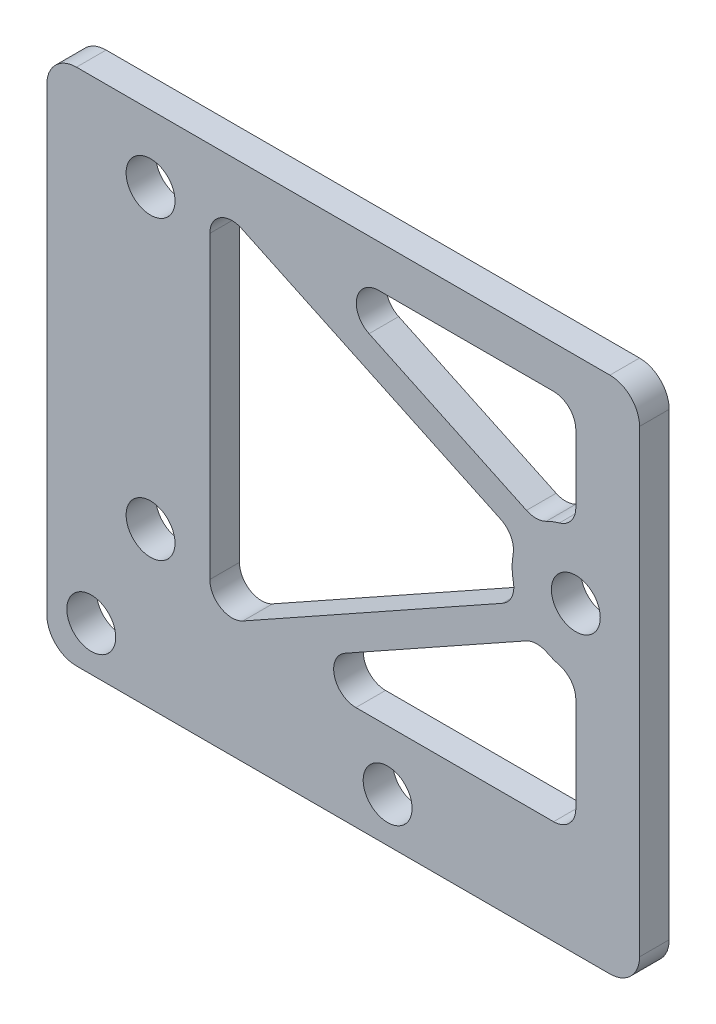
SolidWorks part; units mm, degrees
material "Thornel Mat VMA"
ref_plane "前视基准面" through (0, 0, 0) normal (0, 0, 1) x (1, 0, 0)
ref_plane "上视基准面" through (0, 0, 0) normal (0, 1, 0) x (1, 0, 0)
ref_plane "右视基准面" through (0, 0, 0) normal (1, 0, 0) x (0, 0, -1)
sketch "草图1" plane through (0, 0, 0) normal (0, 0, 1) x (1, 0, 0)
  line L1 (-20, 17.5) -> (20, 17.5)
  line L2 (-20, 17.5) -> (-20, -17.5)
  line L3 (-20, -17.5) -> (20, -17.5)
  line L4 (20, 17.5) -> (20, -17.5)
  line L5 (-20, 17.5) -> (20, -17.5) construction
  line L6 (-20, -17.5) -> (20, 17.5) construction
  point P0 (0, 0)
  dimension "D1" = 40
  dimension "D2" = 35
extrude "凸台-拉伸1" add sketch "草图1" along normal blind 2
sketch "草图2" plane through (0, 0, 2) normal (0, 0, 1) x (1, 0, 0)
  line L0 (-20, -14.5) -> (3, -14.5) construction
  line L1 (-20, 17.5) -> (-20, -17.5) construction
  line L2 (-20, -17.5) -> (20, -17.5) construction
  circle A0 centre (-17, -14.5) radius 1.65
  circle A1 centre (3, -14.5) radius 1.65
  circle A2 centre (-13, -7) radius 1.65
  circle A3 centre (-13, 13) radius 1.65
  circle A4 centre (15.7, 3) radius 1.65
  dimension "D1" = 3.3
  dimension "D3" = 20
  dimension "D5" = 28.7
  dimension "D6" = 4
  dimension "D2" = 3
  dimension "D4" = 10
  dimension "D7" = 3
  dimension "D8" = 20
  dimension "D9" = 7.5
extrude "切除-拉伸1" cut sketch "草图2" against normal blind 2
fillet "圆角1" radius 2 4 edges at (20, -17.5, 1) (20, 17.5, 1) (-20, -17.5, 1) (-20, 17.5, 1)
sketch "草图3" plane through (0, 0, 2) normal (0, 0, 1) x (1, 0, 0)
  line L0 (-9, 14.65) -> (-9, -10.5)
  line L1 (-9, -10.5) -> (11.8235, 1.1392)
  line L2 (11.8109, 4.8343) -> (-9, 14.65)
  line L3 (-4.9008, -10.5) -> (15.7, -10.5)
  line L4 (15.7, -10.5) -> (15.7, -1.3)
  line L5 (13.1103, -0.4327) -> (-4.9008, -10.5)
  line L6 (-4.3117, 14.65) -> (15.7, 14.65)
  line L7 (15.7, 14.65) -> (15.7, 7.3)
  line L8 (13.1103, 6.4327) -> (-4.3117, 14.65)
  circle A0 centre (-13, 13) radius 1.65 construction
  arc A2 (11.8109, 4.8343) -> (11.8235, 1.1392) centre (15.7, 3) ccw
  arc A3 (15.7, 7.3) -> (13.1103, 6.4327) centre (15.7, 3) ccw
  arc A4 (13.1103, -0.4327) -> (15.7, -1.3) centre (15.7, 3) ccw
  circle A5 centre (3, -14.5) radius 1.65 construction
  dimension "D4" = 8.6
  dimension "D1" = 4
  dimension "D2" = 2
  dimension "D3" = 2
  dimension "D5" = 4
extrude "切除-拉伸2" cut sketch "草图3" against normal blind 10
fillet "圆角2" radius 1.5 12 edges at (11.8235, 1.1392, 1) (-9, -10.5, 1) (11.8109, 4.8343, 1) (15.7, 7.3, 1) (13.1103, 6.4327, 1) (-4.3117, 14.65, 1) (15.7, -10.5, 1) (-4.9008, -10.5, 1) (13.1103, -0.4327, 1) (15.7, -1.3, 1) (15.7, 14.65, 1) (-9, 14.65, 1)
